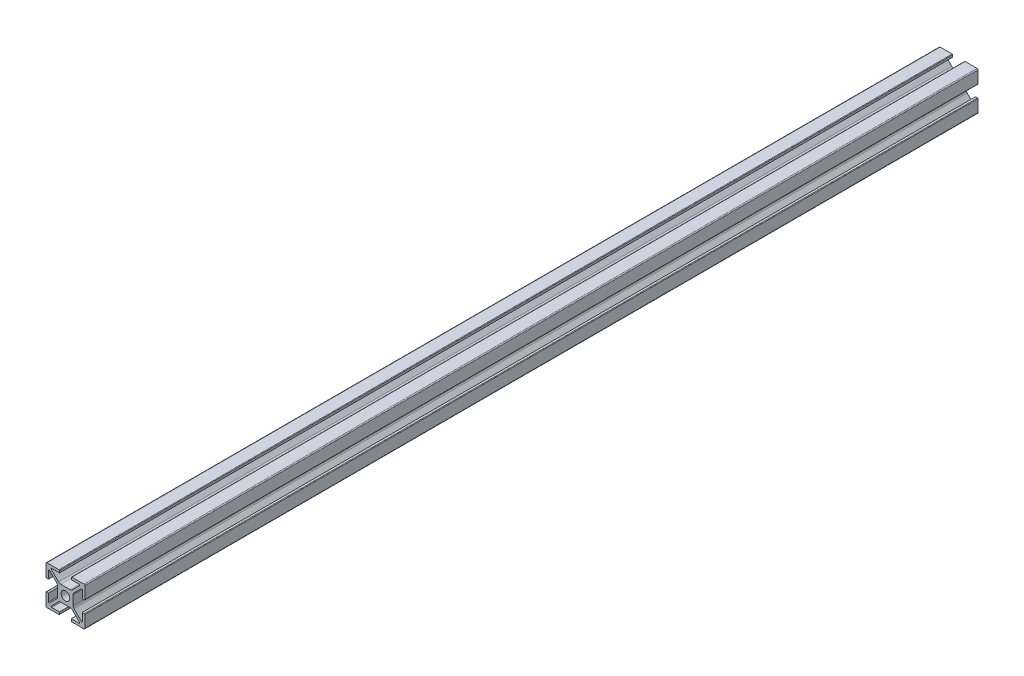
SolidWorks part; units mm, degrees
material "6063-T5"
material "6063-T5"
ref_plane "Front" through (0, 0, 0) normal (0, 0, 1) x (1, 0, 0)
ref_plane "Top" through (0, 0, 0) normal (0, 1, 0) x (1, 0, 0)
ref_plane "Right" through (0, 0, 0) normal (1, 0, 0) x (0, 0, -1)
sketch "Esboço1" plane through (0, 0, 0) normal (1, 0, 0) x (0, 0, -1)
  line L0 (0, 0) -> (-460, 0)
  dimension "D1" = 460
other "Quadrado PF20-21 - PERFIL 2020 T-SLOT 6MM(1)"
ref_plane "Plano1" through (0, 0, 0) normal (0, 0, 1) x (0, -1, 0)
sketch "Esboço11" plane through (0, 0, 0) normal (0, 0, 1) x (0, -1, 0)
  line L0 (8.1879, -7.2686) -> (4.4393, -3.5201)
  line L1 (4, -2.4594) -> (4, 2.4594)
  line L2 (4.4393, 3.5201) -> (8.1879, 7.2686)
  line L3 (8.7, 7.0565) -> (8.7, 3.05)
  line L4 (10, 3.35) -> (10, 9.5)
  line L5 (9.5, 10) -> (3.35, 10)
  line L6 (3.05, 8.7) -> (7.0565, 8.7)
  line L7 (7.2686, 8.1879) -> (3.5201, 4.4393)
  line L8 (2.4594, 4) -> (-2.4594, 4)
  line L9 (-3.5201, 4.4393) -> (-7.2686, 8.1879)
  line L10 (-7.0565, 8.7) -> (-3.05, 8.7)
  line L11 (-3.35, 10) -> (-9.5, 10)
  line L12 (-10, 9.5) -> (-10, 3.35)
  line L13 (-8.7, 3.05) -> (-8.7, 7.0565)
  line L14 (-8.1879, 7.2686) -> (-4.4393, 3.5201)
  line L15 (-4, 2.4594) -> (-4, -2.4594)
  line L16 (-4.4393, -3.5201) -> (-8.1879, -7.2686)
  line L17 (-8.7, -7.0565) -> (-8.7, -3.05)
  line L18 (-10, -3.35) -> (-10, -9.5)
  line L19 (-9.5, -10) -> (-3.35, -10)
  line L20 (-3.05, -8.7) -> (-7.0565, -8.7)
  line L21 (-7.2686, -8.1879) -> (-3.5201, -4.4393)
  line L22 (-2.4594, -4) -> (2.4594, -4)
  line L23 (3.5201, -4.4393) -> (7.2686, -8.1879)
  line L24 (7.0565, -8.7) -> (3.05, -8.7)
  line L25 (3.05, -8.7) -> (3.05, -9.7)
  line L26 (3.35, -10) -> (9.5, -10)
  line L27 (10, -9.5) -> (10, -3.35)
  line L28 (8.7, -3.05) -> (9.7, -3.05)
  line L29 (8.7, -3.05) -> (8.7, -7.0565)
  line L30 (-3.05, 9.7) -> (-3.05, 8.7)
  line L31 (-9.7, -3.05) -> (-8.7, -3.05)
  line L32 (3.05, 9.7) -> (3.05, 8.7)
  line L33 (-9.7, 3.05) -> (-8.7, 3.05)
  line L34 (-3.05, -8.7) -> (-3.05, -9.7)
  line L35 (8.7, 3.05) -> (9.7, 3.05)
  circle A0 centre (0, 0) radius 2.25
  arc A1 (8.1879, -7.2686) -> (8.7, -7.0565) centre (8.4, -7.0565) ccw
  arc A2 (4, -2.4594) -> (4.4393, -3.5201) centre (5.5, -2.4594) ccw
  arc A3 (4.4393, 3.5201) -> (4, 2.4594) centre (5.5, 2.4594) ccw
  arc A4 (8.7, 7.0565) -> (8.1879, 7.2686) centre (8.4, 7.0565) ccw
  arc A5 (10, 9.5) -> (9.5, 10) centre (9.5, 9.5) ccw
  arc A6 (7.2686, 8.1879) -> (7.0565, 8.7) centre (7.0565, 8.4) ccw
  arc A7 (2.4594, 4) -> (3.5201, 4.4393) centre (2.4594, 5.5) ccw
  arc A8 (-3.5201, 4.4393) -> (-2.4594, 4) centre (-2.4594, 5.5) ccw
  arc A9 (-7.0565, 8.7) -> (-7.2686, 8.1879) centre (-7.0565, 8.4) ccw
  arc A10 (-9.5, 10) -> (-10, 9.5) centre (-9.5, 9.5) ccw
  arc A11 (-8.1879, 7.2686) -> (-8.7, 7.0565) centre (-8.4, 7.0565) ccw
  arc A12 (-4, 2.4594) -> (-4.4393, 3.5201) centre (-5.5, 2.4594) ccw
  arc A13 (-4.4393, -3.5201) -> (-4, -2.4594) centre (-5.5, -2.4594) ccw
  arc A14 (-8.7, -7.0565) -> (-8.1879, -7.2686) centre (-8.4, -7.0565) ccw
  arc A15 (-10, -9.5) -> (-9.5, -10) centre (-9.5, -9.5) ccw
  arc A16 (-7.2686, -8.1879) -> (-7.0565, -8.7) centre (-7.0565, -8.4) ccw
  arc A17 (-2.4594, -4) -> (-3.5201, -4.4393) centre (-2.4594, -5.5) ccw
  arc A18 (3.5201, -4.4393) -> (2.4594, -4) centre (2.4594, -5.5) ccw
  arc A19 (7.0565, -8.7) -> (7.2686, -8.1879) centre (7.0565, -8.4) ccw
  arc A20 (9.5, -10) -> (10, -9.5) centre (9.5, -9.5) ccw
  arc A21 (-9.7, 3.05) -> (-10, 3.35) centre (-9.7, 3.35) cw
  arc A22 (-9.7, -3.05) -> (-10, -3.35) centre (-9.7, -3.35) ccw
  arc A23 (-3.05, -9.7) -> (-3.35, -10) centre (-3.35, -9.7) cw
  arc A24 (3.05, -9.7) -> (3.35, -10) centre (3.35, -9.7) ccw
  arc A25 (9.7, -3.05) -> (10, -3.35) centre (9.7, -3.35) cw
  arc A26 (9.7, 3.05) -> (10, 3.35) centre (9.7, 3.35) ccw
  arc A27 (3.05, 9.7) -> (3.35, 10) centre (3.35, 9.7) cw
  arc A28 (-3.05, 9.7) -> (-3.35, 10) centre (-3.35, 9.7) ccw
  point P0 (0, 10)
  point P1 (-10, 10)
  point P2 (0, 0)
  point P3 (10, 10)
  point P4 (10, 0)
  point P5 (10, -10)
  point P6 (0, -10)
  point P7 (-10, -10)
  point P8 (-10, 0)
  point P9 (0, 0)
  point P88 (0, 0)
